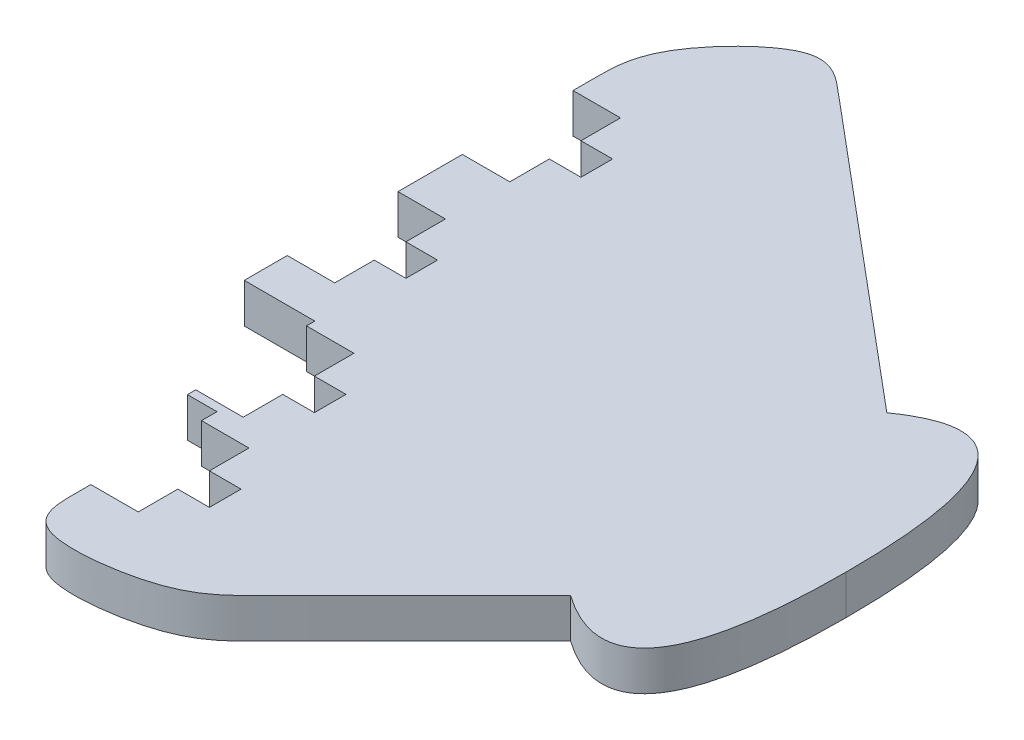
SolidWorks part; units mm, degrees
ref_plane "Front Plane" through (0, 0, 0) normal (0, 0, 1) x (1, 0, 0)
ref_plane "Top Plane" through (0, 0, 0) normal (0, 1, 0) x (1, 0, 0)
ref_plane "Right Plane" through (0, 0, 0) normal (1, 0, 0) x (0, 0, -1)
sketch "Sketch1" plane through (0, 0, 0) normal (0, 1, 0) x (1, 0, 0)
  line L0 (0, 0) -> (0, 20) construction
  line L1 (0, 0) -> (0, -20) construction
  line L2 (0, 0) -> (45, 0) construction
  line L3 (0, 20) -> (40, 20) construction
  line L4 (0, -20) -> (40, -20) construction
  line L5 (45, 22.5) -> (45, 0) construction
  line L6 (45, 0) -> (45, -22.5) construction
  line L7 (45, 0) -> (54.8646, 0) construction
  line L8 (40, 20) -> (1.6978, 52.1394) construction
  line L9 (54.8646, 40.627) -> (54.8646, -46.0883) construction
  line L10 (-15.1354, 38.1539) -> (54.8646, 0) construction
  line L11 (-15.1354, -6.1242) -> (54.8646, 0) construction
  line L12 (-15.1354, 18.7564) -> (54.8646, 0) construction
  line L13 (-6.2154, -22.2313) -> (54.8646, 0) construction
  line L14 (-2.4761, -40.1504) -> (54.8646, 0) construction
  line L15 (-0.2154, -7.1778) -> (-0.2154, -12.1778)
  line L16 (-15.1354, 38.1539) -> (-15.1354, 35.4552) construction
  line L17 (-2.4761, -38.1908) -> (-2.4761, -40.1504) construction
  line L18 (-0.2154, -21.1778) -> (-0.2154, -16.1778)
  line L19 (-15.1354, 35.4552) -> (-9.1354, 35.4552)
  line L20 (-9.1354, 35.4552) -> (-9.1354, 30.4552)
  line L21 (-15.1354, -6.1242) -> (-6.2154, -6.1242)
  line L25 (19.8496, -40.1504) -> (40, -20) construction
  line L27 (-15.1354, 18.7564) -> (-15.1354, 21.4552)
  line L28 (-15.1354, 18.7564) -> (-15.1354, 13.3161)
  line L29 (-15.1354, 13.3161) -> (-9.1354, 13.3161)
  line L30 (-9.1354, 30.4552) -> (-5.1354, 30.4552)
  line L31 (-9.1354, -0.6839) -> (-15.1354, -0.6839)
  line L32 (-15.1354, -0.6839) -> (-15.1354, -6.1242)
  line L33 (-15.1354, 21.4552) -> (-9.1354, 21.4552)
  line L34 (-5.1354, 30.4552) -> (-5.1354, 26.4552)
  line L35 (-5.1354, 26.4552) -> (-9.1354, 26.4552)
  line L36 (-9.1354, 26.4552) -> (-9.1354, 21.4552)
  line L37 (-9.1354, 13.3161) -> (-9.1354, 8.3161)
  line L38 (-9.1354, 8.3161) -> (-5.1354, 8.3161)
  line L39 (-5.1354, 8.3161) -> (-5.1354, 4.3161)
  line L40 (-5.1354, 4.3161) -> (-9.1354, 4.3161)
  line L41 (-9.1354, 4.3161) -> (-9.1354, -0.6839)
  line L42 (-6.2154, -6.1242) -> (-6.2154, -7.1778)
  line L43 (-6.2154, -22.2313) -> (-2.4761, -22.2313)
  line L44 (-2.4761, -22.2313) -> (-2.4761, -24.1908)
  line L45 (-6.2154, -7.1778) -> (-0.2154, -7.1778)
  line L47 (-0.2154, -16.1778) -> (3.7846, -16.1778)
  line L48 (3.7846, -16.1778) -> (3.7846, -12.1778)
  line L49 (3.7846, -12.1778) -> (-0.2154, -12.1778)
  line L51 (-0.2154, -21.1778) -> (-6.2154, -21.1778)
  line L52 (-6.2154, -21.1778) -> (-6.2154, -22.2313)
  line L53 (-2.4761, -24.1908) -> (3.5239, -24.1908)
  line L54 (3.5239, -24.1908) -> (3.5239, -29.1908)
  line L55 (3.5239, -29.1908) -> (7.5239, -29.1908)
  line L56 (7.5239, -29.1908) -> (7.5239, -33.1908)
  line L57 (7.5239, -33.1908) -> (3.5239, -33.1908)
  line L58 (3.5239, -33.1908) -> (3.5239, -38.1908)
  line L59 (3.5239, -38.1908) -> (-2.4761, -38.1908)
  spline S0 degree 2 poles (54.8646, 0) (54.8646, 30.5533) (40, 20) knots 0 0 0 1 1 1
  spline S1 degree 2 poles (54.8646, 0) (54.8646, -30.5533) (40, -20) knots 0 0 0 1 1 1
  spline S2 degree 3 poles (-2.4761, -38.1908) (-2.4761, -38.844) (-2.4761, -39.4972) (-2.4761, -40.1504) (-2.4761, -42.631) (-2.4761, -47.5923) (14.5874, -45.4126) (18.0956, -41.9044) (19.8496, -40.1504) (26.5664, -33.4336) (33.2832, -26.7168) (40, -20) knots 0 0 0 0 0.037125 0.037125 0.037125 0.178118 0.31911 0.460103 0.460103 0.460103 1 1 1 1
  spline S3 degree 3 poles (40, 20) (27.2326, 30.7131) (14.4652, 41.4263) (1.6978, 52.1394) (-0.165, 53.7024) (-3.8905, 56.8285) (-15.1354, 45.4489) (-15.1354, 40.5856) (-15.1354, 38.1539) (-15.1354, 37.2544) (-15.1354, 36.3548) (-15.1354, 35.4552) knots 0 0 0 0 0.670388 0.670388 0.670388 0.768197 0.866007 0.963816 0.963816 0.963816 1 1 1 1
  dimension "D1" = 45
  dimension "D2" = 40
  dimension "D4" = 45
  dimension "D5" = 5
  dimension "D6" = 40
  dimension "D7" = 50
  dimension "D8" = 14
  dimension "D9" = 70
  dimension "D10" = 5
  dimension "D11" = 15
  dimension "D12" = 65
  dimension "D13" = 6
  dimension "D14" = 20
  dimension "D15" = 35
  dimension "D16" = 6
  dimension "D17" = 4
  dimension "D18" = 4
  dimension "D20" = 45
  dimension "D21" = 4
  dimension "D22" = 4
  dimension "D23" = 4
  dimension "D25" = 14
  dimension "D26" = 4
  dimension "D27" = 70
extrude "Boss-Extrude1" add sketch "Sketch1" along normal blind 5
